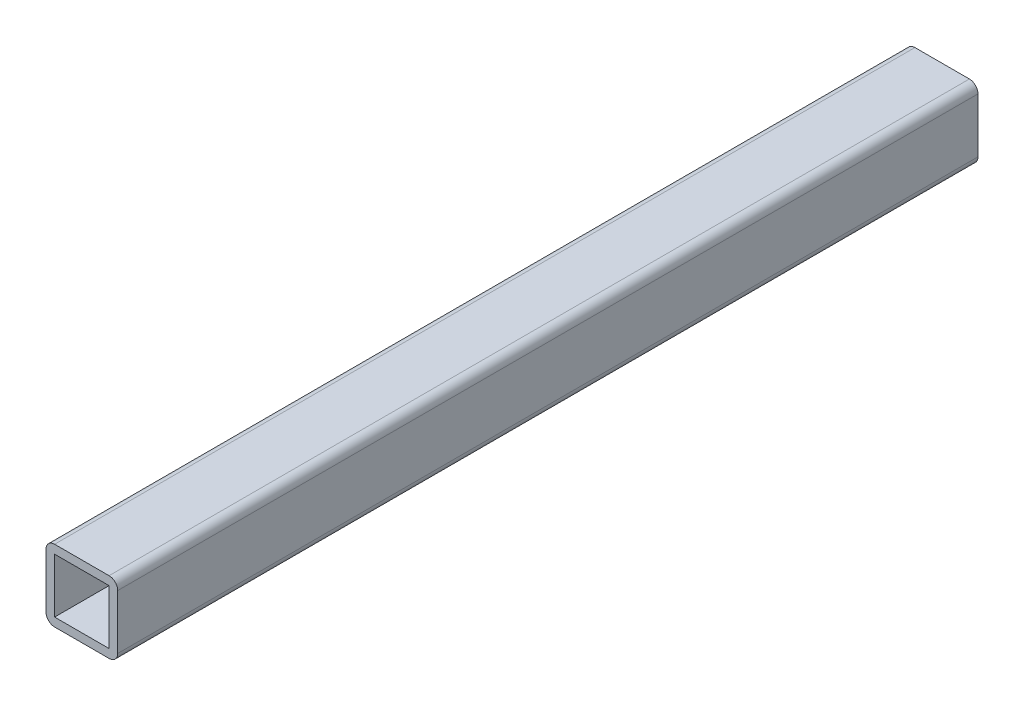
SolidWorks part; units mm, degrees
material "ASTM A36 Steel"
ref_plane "Front Plane" through (0, 0, 0) normal (0, 0, 1) x (1, 0, 0)
ref_plane "Top Plane" through (0, 0, 0) normal (0, 1, 0) x (1, 0, 0)
ref_plane "Right Plane" through (0, 0, 0) normal (1, 0, 0) x (0, 0, -1)
sketch "Sketch1" plane through (0, 0, 0) normal (0, 0, 1) x (1, 0, 0)
  line L0 (-9.5, 9.5) -> (9.5, 9.5)
  line L1 (-9.5, -12.5) -> (9.5, -12.5)
  line L2 (-12.5, -9.5) -> (-12.5, 9.5)
  line L3 (-9.5, 12.5) -> (9.5, 12.5)
  line L4 (12.5, -9.5) -> (12.5, 9.5)
  line L5 (-12.5, -12.5) -> (12.5, 12.5) construction
  line L6 (-12.5, 12.5) -> (12.5, -12.5) construction
  line L7 (9.5, -9.5) -> (9.5, 9.5)
  line L8 (-9.5, -9.5) -> (9.5, -9.5)
  line L9 (-9.5, -9.5) -> (-9.5, 9.5)
  arc A0 (-12.5, -9.5) -> (-9.5, -12.5) centre (-9.5, -9.5) ccw
  arc A1 (9.5, -12.5) -> (12.5, -9.5) centre (9.5, -9.5) ccw
  arc A2 (12.5, 9.5) -> (9.5, 12.5) centre (9.5, 9.5) ccw
  arc A3 (-12.5, 9.5) -> (-9.5, 12.5) centre (-9.5, 9.5) cw
  arc A4 (9.5, 9.5) -> (9.5, 9.5) centre (9.5, 9.5) ccw
  arc A5 (9.5, -9.5) -> (9.5, -9.5) centre (9.5, -9.5) ccw
  arc A6 (-9.5, -9.5) -> (-9.5, -9.5) centre (-9.5, -9.5) ccw
  arc A7 (-9.5, 9.5) -> (-9.5, 9.5) centre (-9.5, 9.5) cw
  point P0 (0, 0)
  dimension "D2" = 3
  dimension "D1" = 25
  dimension "D3" = 3
extrude "Boss-Extrude1" add sketch "Sketch1" along normal blind 300
